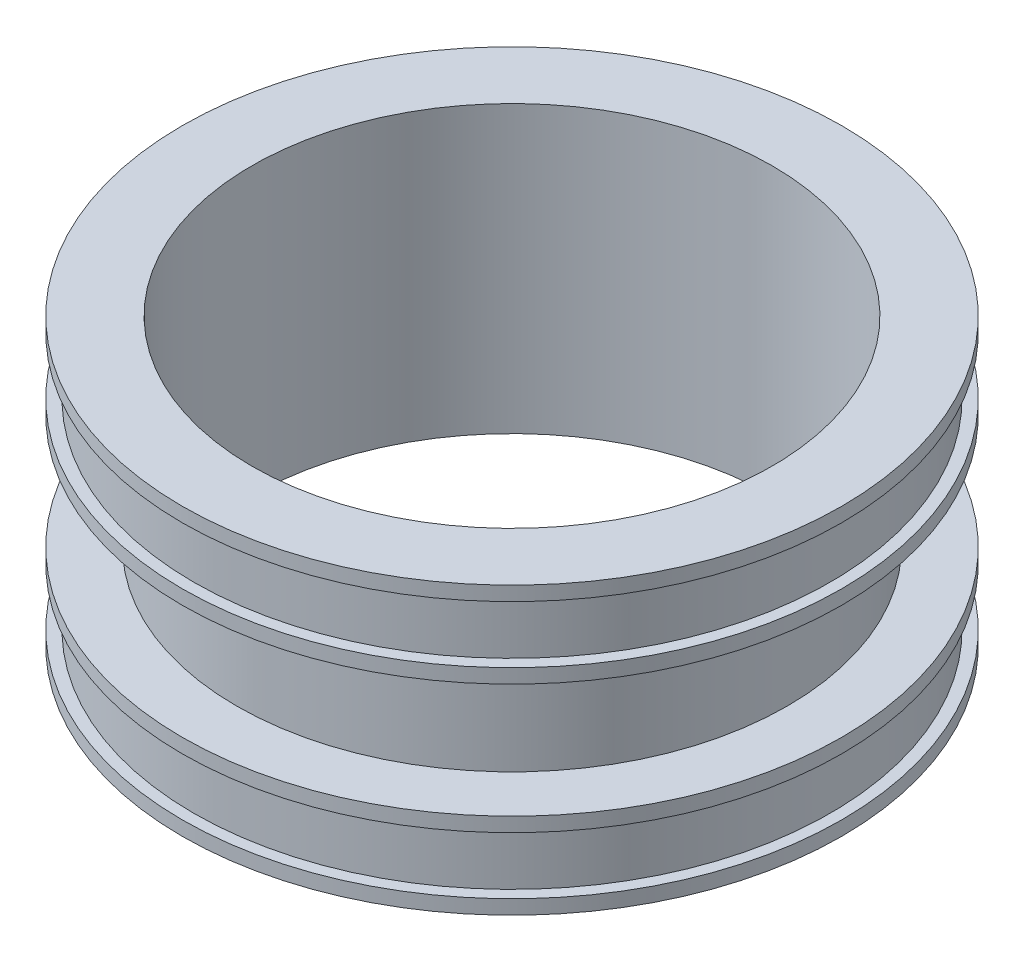
SolidWorks part; units mm, degrees
material "AISI 1020"
ref_plane "Plano frontal" through (0, 0, 0) normal (0, 0, 1) x (1, 0, 0)
ref_plane "Plano superior" through (0, 0, 0) normal (0, 1, 0) x (1, 0, 0)
ref_plane "Plano direito" through (0, 0, 0) normal (1, 0, 0) x (0, 0, -1)
sketch "Esboço1" plane through (0, 0, 0) normal (0, 0, 1) x (1, 0, 0)
  line L0 (0, 0) -> (0, 327.1613) construction
  line L1 (0, 0) -> (502.3995, 0) construction
  line L2 (136.525, 150) -> (173, 150)
  line L3 (173, 150) -> (173, 142.5)
  line L4 (173, 105) -> (144.525, 105)
  line L5 (144.525, 105) -> (144.525, 45)
  line L6 (144.525, 45) -> (173, 45)
  line L7 (173, 45) -> (173, 37.5)
  line L8 (173, 0) -> (136.525, 0)
  line L9 (136.525, 0) -> (136.525, 150)
  line L10 (173, 142.5) -> (167, 142.5)
  line L11 (167, 142.5) -> (167, 112.5)
  line L12 (167, 112.5) -> (173, 112.5)
  line L13 (136.525, 75) -> (173, 75) construction
  line L14 (173, 112.5) -> (173, 105)
  line L15 (167, 37.5) -> (173, 37.5)
  line L16 (167, 7.5) -> (167, 37.5)
  line L17 (173, 7.5) -> (167, 7.5)
  line L18 (173, 7.5) -> (173, 0)
  point P22 (144.525, 75)
  dimension "D1" = 273.05
  dimension "D2" = 6
  dimension "D3" = 30
  dimension "D4" = 45
  dimension "250" = 346
  dimension "D6" = 8
  dimension "D7" = 150
revolve "Revolução1" add sketch "Esboço1" angle 360 about L0
